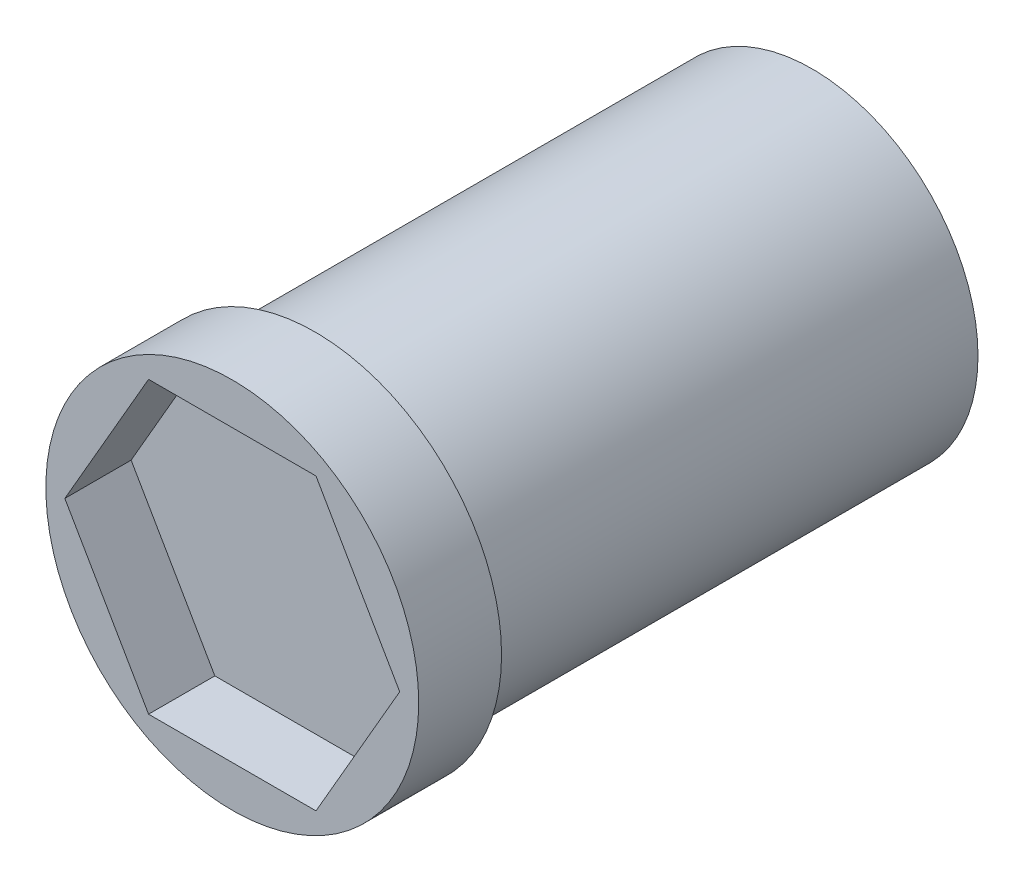
SolidWorks part; units mm, degrees
ref_plane "Front Plane" through (0, 0, 0) normal (0, 0, 1) x (1, 0, 0)
ref_plane "Top Plane" through (0, 0, 0) normal (0, 1, 0) x (1, 0, 0)
ref_plane "Right Plane" through (0, 0, 0) normal (1, 0, 0) x (0, 0, -1)
sketch "Sketch1" plane through (0, 0, 0) normal (0, 0, 1) x (1, 0, 0)
  circle A0 centre (0, 0) radius 20
  dimension "D1" = 40
extrude "Boss-Extrude1" add sketch "Sketch1" along normal blind 60
sketch "Sketch2" plane through (0, 0, 60) normal (0, 0, 1) x (1, 0, 0)
  circle A0 centre (0, 0) radius 22.5
  dimension "D1" = 45
extrude "Boss-Extrude2" add sketch "Sketch2" along normal blind 10
sketch "Sketch3" plane through (0, 0, 70) normal (0, 0, 1) x (1, 0, 0)
  line L1 (-20.2073, 0) -> (-10.1036, -17.5)
  line L2 (-10.1036, -17.5) -> (10.1036, -17.5)
  line L3 (10.1036, -17.5) -> (20.2073, 0)
  line L4 (20.2073, 0) -> (10.1036, 17.5)
  line L5 (10.1036, 17.5) -> (-10.1036, 17.5)
  line L6 (-10.1036, 17.5) -> (-20.2073, 0)
  circle A0 centre (0, 0) radius 17.5 construction
  point P1 (0, 17.5)
  dimension "D1" = 35
extrude "Cut-Extrude1" cut sketch "Sketch3" against normal blind 8
